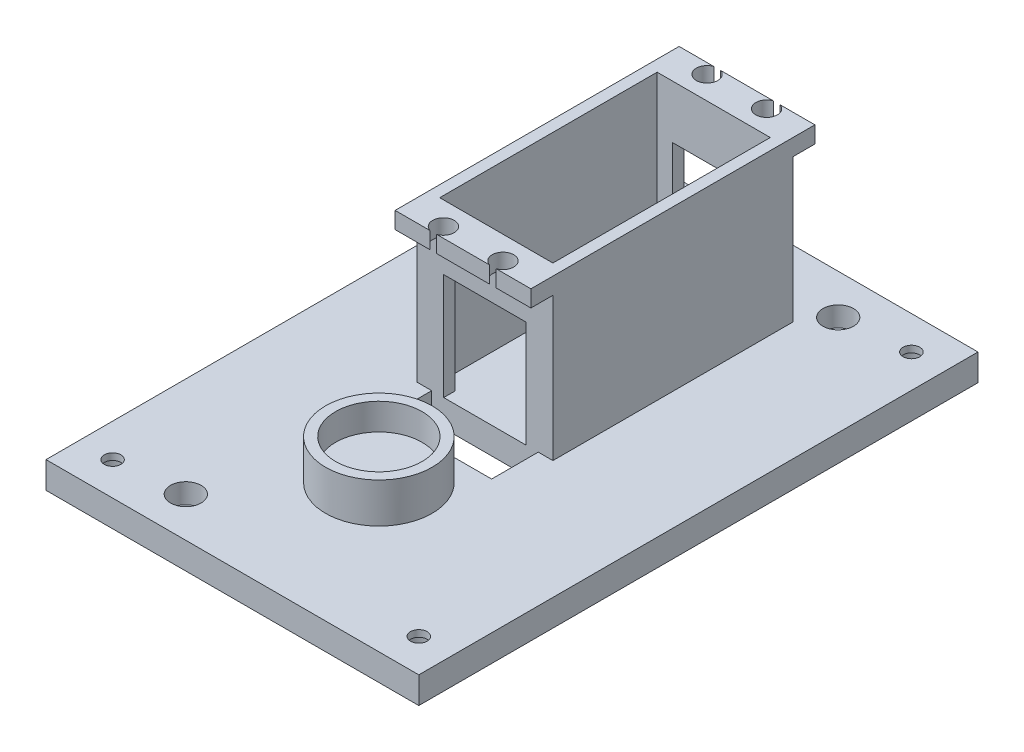
SolidWorks part; units mm, degrees
other "Markup1"
sketch "Sketch13" plane through (63.4306, 35.56, -46.9233) normal (0.8871, 0.4534, -0.0863) x (0.4601, -0.8836, 0.0876)
sketch "Sketch14" plane through (63.4306, 35.56, -46.9233) normal (0.8871, 0.4534, -0.0863) x (0.4601, -0.8836, 0.0876)
sketch "Sketch18" plane through (63.4306, 35.56, -46.9233) normal (0.8871, 0.4534, -0.0863) x (0.4601, -0.8836, 0.0876)
sketch "Sketch19" plane through (63.4306, 35.56, -46.9233) normal (0.8871, 0.4534, -0.0863) x (0.4601, -0.8836, 0.0876)
sketch "Sketch20" plane through (63.4306, 35.56, -46.9233) normal (0.8871, 0.4534, -0.0863) x (0.4601, -0.8836, 0.0876)
ref_plane "Front Plane" through (0, 0, 0) normal (0, 0, 1) x (1, 0, 0)
ref_plane "Top Plane" through (0, 0, 0) normal (0, 1, 0) x (1, 0, 0)
ref_plane "Right Plane" through (0, 0, 0) normal (1, 0, 0) x (0, 0, -1)
sketch "Sketch1" plane through (56.4019, 0, 2.6132) normal (0, 1, 0) x (1, 0, 0)
  line L1 (-64.0913, -57.1435) -> (7.0287, -57.1435)
  line L2 (-64.0913, -57.1435) -> (-64.0913, 49.5365)
  line L3 (-64.0913, 49.5365) -> (7.0287, 49.5365)
  line L4 (7.0287, -57.1435) -> (7.0287, 49.5365)
  dimension "D1" = 71.12
  dimension "D2" = 106.68
extrude "Boss-Extrude1" add sketch "Sketch1" along normal blind 5.08
sketch "Sketch3" plane through (56.4019, 5.08, 2.6132) normal (0, 1, 0) x (1, 0, 0)
  line L1 (-17.7363, 34.6775) -> (-39.3263, 34.6775)
  line L2 (-17.7363, 34.6775) -> (-17.7363, -6.8007)
  line L3 (-17.7363, -6.8007) -> (-39.3263, -6.8007)
  line L4 (-39.3263, 34.6775) -> (-39.3263, -6.8007)
  line L5 (-41.4853, 36.8365) -> (-15.5773, 36.8365)
  line L6 (-41.4853, 36.8365) -> (-41.4853, -8.9597)
  line L7 (-41.4853, -8.9597) -> (-15.5773, -8.9597)
  line L8 (-15.5773, 36.8365) -> (-15.5773, -8.9597)
  line L9 (7.0287, 49.5365) -> (-64.0913, 49.5365) construction
  point P5 (-28.5313, 36.8365)
  point P8 (-28.5313, 49.5365)
  dimension "D1" = 21.59
  dimension "D2" = 41.4782
  dimension "D4" = 2.159
  dimension "D5" = 2.159
  dimension "D6" = 2.159
  dimension "D7" = 2.159
  dimension "D8" = 12.7
extrude "Boss-Extrude2" add sketch "Sketch3" along normal blind 27.305
sketch "Sketch4" plane through (0, 32.385, 0) normal (0, 1, 0) x (1, 0, 0)
  line L0 (40.8246, -11.5729) -> (40.8246, 34.2233) construction
  line L1 (17.0756, 32.0643) -> (38.6656, 32.0643)
  line L2 (17.0756, 32.0643) -> (17.0756, -9.4139)
  line L3 (17.0756, -9.4139) -> (38.6656, -9.4139)
  line L4 (38.6656, 32.0643) -> (38.6656, -9.4139)
  line L5 (14.9166, 38.4143) -> (40.8246, 38.4143)
  line L6 (14.9166, 38.4143) -> (14.9166, -15.7639)
  line L7 (14.9166, -15.7639) -> (40.8246, -15.7639)
  line L8 (40.8246, 38.4143) -> (40.8246, -15.7639)
  line L10 (14.9166, 34.2233) -> (14.9166, -11.5729) construction
  dimension "D1" = 6.35
  dimension "D2" = 6.35
extrude "Boss-Extrude3" add sketch "Sketch4" along normal blind 3.175
sketch "Sketch5" plane through (0, 35.56, 0) normal (0, 1, 0) x (1, 0, 0)
  line L0 (40.8246, -15.7639) -> (40.8246, 38.4143) construction
  line L2 (27.8706, 32.0643) -> (27.8706, 42.675) construction
  line L3 (38.6656, 32.0643) -> (17.0756, 32.0643) construction
  circle A0 centre (22.1937, 36.4712) radius 2.0497
  circle A1 centre (33.5475, 36.4712) radius 2.0497
  circle A2 centre (22.1937, -13.8208) radius 2.0497
  circle A3 centre (33.5475, -13.8208) radius 2.0497
  point P10 (40.8246, 11.3252)
  dimension "D1" = 4.0994
  dimension "D5" = 5.6769
  dimension "D2" = 11.3538
  dimension "D3" = 11.3538
  dimension "D4" = 5.6769
  dimension "D6" = 50.292
  dimension "D7" = 25.146
extrude "Cut-Extrude1" cut sketch "Sketch5" against normal blind 3.175
sketch "Sketch7" plane through (0, 0, -34.2233) normal (0, 0, -1) x (-1, 0, 0)
  line L0 (-40.8246, 5.08) -> (-14.9166, 5.08) construction
  line L1 (-35.7446, 5.08) -> (-19.9966, 5.08)
  line L2 (-35.7446, 5.08) -> (-35.7446, 25.4)
  line L3 (-35.7446, 25.4) -> (-19.9966, 25.4)
  line L4 (-19.9966, 5.08) -> (-19.9966, 25.4)
  line L5 (-40.8246, 32.385) -> (-40.8246, 5.08) construction
  line L6 (-14.9166, 32.385) -> (-14.9166, 5.08) construction
  dimension "D1" = 5.08
  dimension "D2" = 5.08
  dimension "D3" = 20.32
extrude "Cut-Extrude3" cut sketch "Sketch7" against normal up to surface (45.7962 mm away) up to face at (27.8706, 18.7325, 11.5729)
sketch "Sketch8" plane through (0, 5.08, 0) normal (0, 1, 0) x (1, 0, 0)
  line L0 (63.4306, 46.9233) -> (-7.6894, 46.9233) construction
  circle A0 centre (27.8706, -31.8167) radius 10.16
  point P4 (27.8706, 46.9233)
  dimension "D1" = 20.32
  dimension "D2" = 78.74
extrude "Boss-Extrude4" add sketch "Sketch8" along normal blind 7.62
sketch "Sketch9" plane through (0, 12.7, 0) normal (0, 1, 0) x (1, 0, 0)
  circle A0 centre (27.8706, -31.8167) radius 8.255
  dimension "D1" = 16.51
extrude "Cut-Extrude4" cut sketch "Sketch9" against normal blind 5.08 contours A0
sketch "Sketch10" plane through (0, 5.08, 0) normal (0, 1, 0) x (1, 0, 0)
  line L1 (17.7106, -11.5729) -> (38.0306, -11.5729)
  line L2 (17.7106, -11.5729) -> (17.7106, -20.4629)
  line L3 (17.7106, -20.4629) -> (38.0306, -20.4629)
  line L4 (38.0306, -11.5729) -> (38.0306, -20.4629)
  line L5 (63.4306, 46.9233) -> (-7.6894, 46.9233) construction
  line L6 (35.7446, -11.5729) -> (40.8246, -11.5729) construction
  point P8 (27.8706, -11.5729)
  point P9 (27.8706, 46.9233)
  dimension "D1" = 20.32
  dimension "D3" = 8.89
extrude "Cut-Extrude5" cut sketch "Sketch10" against normal through all
sketch "Sketch11" plane through (0, 5.08, 0) normal (0, 1, 0) x (1, 0, 0)
  line L0 (63.4306, 46.9233) -> (-7.6894, 46.9233) construction
  line L1 (-7.6894, -59.7567) -> (63.4306, -59.7567) construction
  line L2 (63.4306, -59.7567) -> (63.4306, 46.9233) construction
  line L3 (-7.6894, 46.9233) -> (-7.6894, -59.7567) construction
  circle A0 centre (44.3806, 39.3033) radius 1.5875
  circle A1 centre (11.3606, -52.1367) radius 1.5875
  dimension "D1" = 3.175
  dimension "D2" = 3.175
  dimension "D3" = 7.62
  dimension "D4" = 7.62
  dimension "D5" = 19.05
  dimension "D6" = 19.05
extrude "Cut-Extrude6" cut sketch "Sketch11" against normal through all
sketch "Sketch15" plane through (0, 5.08, 0) normal (0, 1, 0) x (1, 0, 0)
  circle A0 centre (11.3606, -52.1367) radius 2.921
  circle A1 centre (44.3806, 39.3033) radius 2.921
  dimension "D1" = 5.842
  dimension "D2" = 5.842
extrude "Cut-Extrude7" cut sketch "Sketch15" against normal blind 3.81
sketch "Sketch16" plane through (0, 0, 0) normal (0, -1, 0) x (1, 0, 0)
  line L0 (-7.6894, 59.7567) -> (63.4306, 59.7567) construction
  line L1 (-7.6894, -46.9233) -> (-7.6894, 59.7567) construction
  circle A0 centre (-1.3394, 53.4067) radius 2.921
  circle A1 centre (57.0806, 53.4067) radius 2.921
  circle A2 centre (57.0806, -40.5733) radius 2.921
  circle A3 centre (-1.3394, -40.5733) radius 2.921
  dimension "D1" = 6.35
  dimension "D5" = 5.842
  dimension "D2" = 6.35
  dimension "D3" = 2
  dimension "D4" = 2
extrude "Cut-Extrude8" cut sketch "Sketch16" against normal blind 3.81
sketch "Sketch17" plane through (0, 0, 0) normal (0, -1, 0) x (1, 0, 0)
  circle A0 centre (-1.3394, 53.4067) radius 1.5875
  circle A1 centre (57.0806, 53.4067) radius 1.5875
  circle A2 centre (57.0806, -40.5733) radius 1.5875
  circle A3 centre (-1.3394, -40.5733) radius 1.5875
  dimension "D1" = 2
  dimension "D3" = 3.175
  dimension "D2" = 2
extrude "Cut-Extrude9" cut sketch "Sketch17" against normal through all
